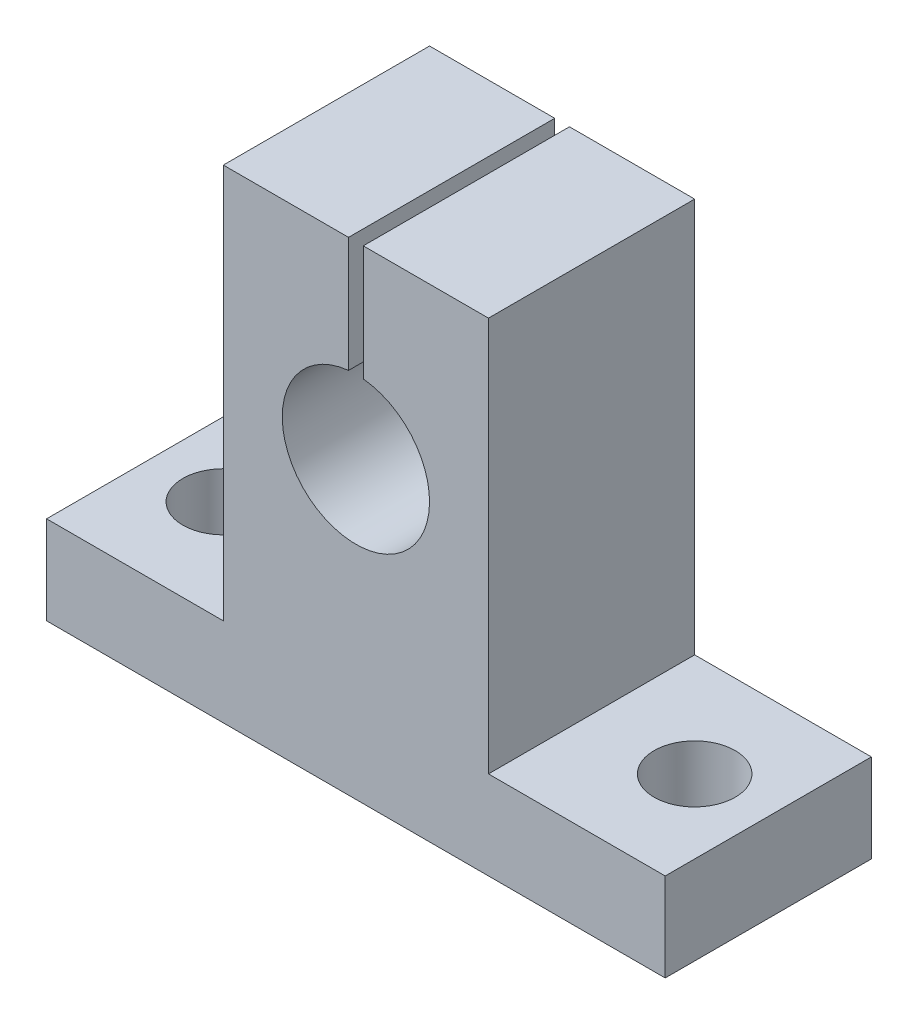
SolidWorks part; units mm, degrees
ref_plane "Front Plane" through (0, 0, 0) normal (0, 0, 1) x (1, 0, 0)
ref_plane "Top Plane" through (0, 0, 0) normal (0, 1, 0) x (1, 0, 0)
ref_plane "Right Plane" through (0, 0, 0) normal (1, 0, 0) x (0, 0, -1)
sketch "Sketch1" plane through (0, 0, 0) normal (0, 0, 1) x (1, 0, 0)
  line L0 (0, 12.8) -> (0, -20) construction
  line L1 (9, 12.8) -> (-9, 12.8)
  line L2 (-9, 12.8) -> (-9, -14)
  line L3 (-9, -14) -> (-21, -14)
  line L4 (-21, -14) -> (-21, -20)
  line L5 (-21, -20) -> (21, -20)
  line L6 (21, -14) -> (21, -20)
  line L7 (9, -14) -> (21, -14)
  line L8 (9, 12.8) -> (9, -14)
  circle A0 centre (0, 0) radius 5
  dimension "D1" = 10
  dimension "D2" = 18
  dimension "D3" = 42
  dimension "D4" = 32.8
  dimension "D5" = 20
  dimension "D6" = 6
extrude "Boss-Extrude1" add sketch "Sketch1" along normal blind 14
sketch "Sketch2" plane through (0, 0, 14) normal (0, 0, 1) x (1, 0, 0)
  line L2 (0.5, -0.6708) -> (-0.5, -0.6708)
  line L3 (0.5, -0.6708) -> (0.5, 14.6769)
  line L4 (0.5, 14.6769) -> (-0.5, 14.6769)
  line L5 (-0.5, -0.6708) -> (-0.5, 14.6769)
  line L6 (0.5, -0.6708) -> (-0.5, 14.6769) construction
  line L7 (0.5, 14.6769) -> (-0.5, -0.6708) construction
  point P0 (0, 7.0031)
  point P6 (0, 0)
extrude "Cut-Extrude1" cut sketch "Sketch2" against normal through all
sketch "Sketch3" plane through (0, -14, 0) normal (0, 1, 0) x (1, 0, 0)
  line L0 (0, 0) -> (0, -14) construction
  line L1 (-5, -14) -> (5, -14) construction
  circle A0 centre (-16, -7) radius 2.75
  circle A1 centre (16, -7) radius 2.75
  point P7 (0, 0)
  point P8 (0, 0)
  point P9 (0, -7)
  dimension "D1" = 5.5
  dimension "D2" = 32
extrude "Cut-Extrude2" cut sketch "Sketch3" against normal through all
